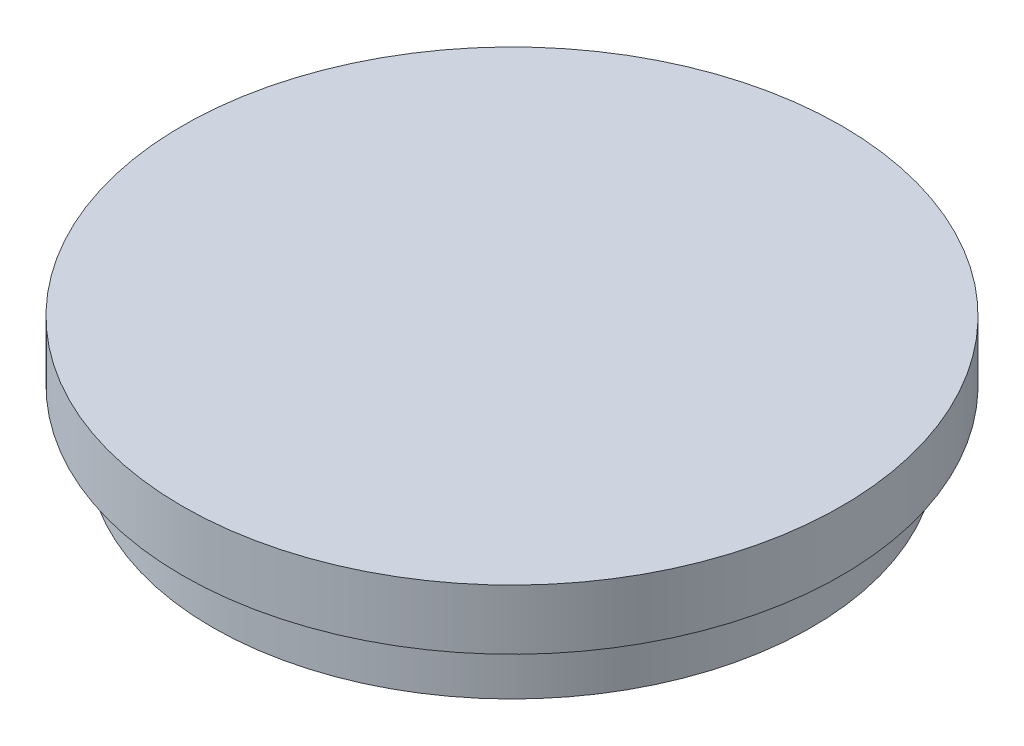
SolidWorks part; units mm, degrees
ref_plane "Front Plane" through (0, 0, 0) normal (0, 0, 1) x (1, 0, 0)
ref_plane "Top Plane" through (0, 0, 0) normal (0, 1, 0) x (1, 0, 0)
ref_plane "Right Plane" through (0, 0, 0) normal (1, 0, 0) x (0, 0, -1)
sketch "Sketch1" plane through (0, 0, 0) normal (0, 1, 0) x (1, 0, 0)
  circle A0 centre (0, 0) radius 10
  dimension "D1" = 20
extrude "Boss-Extrude1" add sketch "Sketch1" along normal blind 2
sketch "Sketch2" plane through (0, 2, 0) normal (0, 1, 0) x (1, 0, 0)
  circle A0 centre (0, 0) radius 11
  dimension "D1" = 22
extrude "Boss-Extrude2" add sketch "Sketch2" along normal blind 2
